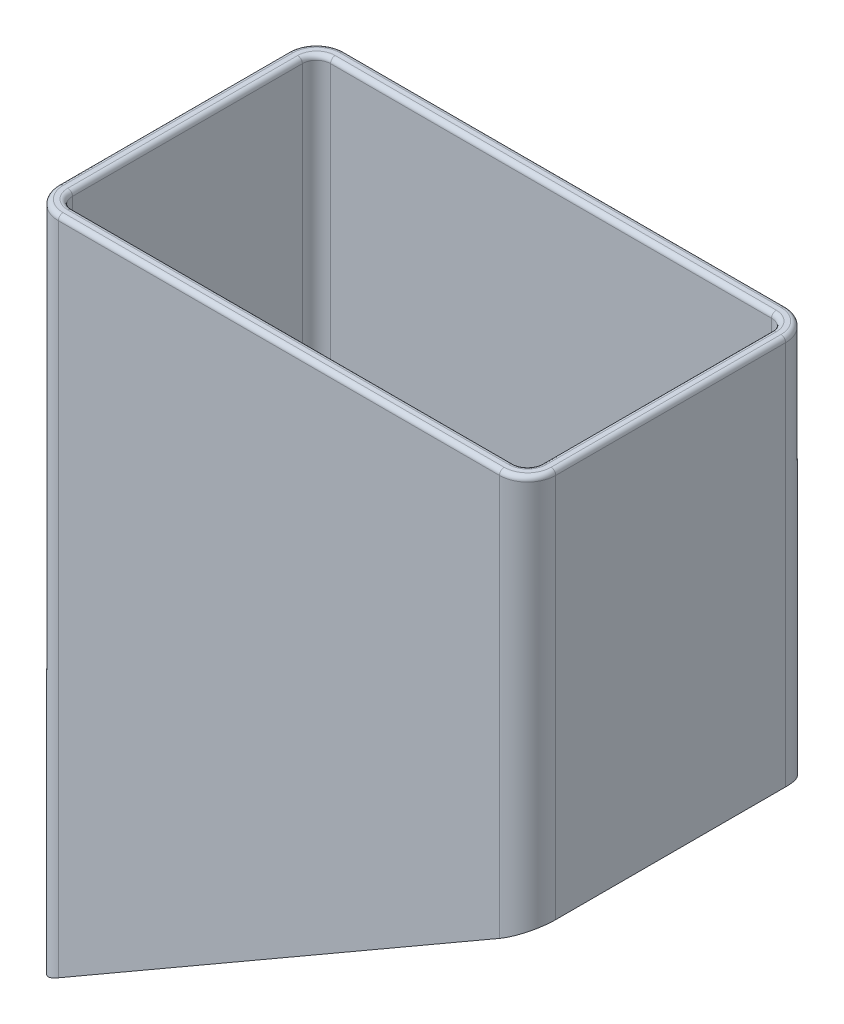
SolidWorks part; units mm, degrees
ref_plane "Front Plane" through (0, 0, 0) normal (0, 0, 1) x (1, 0, 0)
ref_plane "Top Plane" through (0, 0, 0) normal (0, 1, 0) x (1, 0, 0)
ref_plane "Right Plane" through (0, 0, 0) normal (1, 0, 0) x (0, 0, -1)
sketch "Sketch1" plane through (0, 0, 0) normal (0, 0, 1) x (1, 0, 0)
  line L0 (-50, 80) -> (-50, 0)
  line L1 (-50, 80) -> (50, 80)
  line L2 (-50, 0) -> (50, 0)
  line L3 (50, 80) -> (50, 0)
  line L4 (-50, 80) -> (50, 0) construction
  line L5 (-50, 0) -> (50, 80) construction
  line L6 (50, 80) -> (53, 80)
  line L7 (53, 80) -> (53, -3)
  line L8 (53, -3) -> (-53, -3)
  line L9 (-53, -3) -> (-53, 80)
  line L10 (-53, 80) -> (-50, 80)
  line L12 (-53, -3) -> (-50, -3) construction
  line L13 (-53, -3) -> (-53, 0) construction
  line L14 (-53, 0) -> (-50, 0) construction
  line L15 (-50, -3) -> (-50, 0) construction
  point P0 (32.4033, -1.1295)
  point P1 (0, 40)
  point P10 (-12.1047, -2.4419)
  point P13 (-8.686, -0.4186)
  point P14 (0, 0)
  dimension "D1" = 3
  dimension "D2" = 100
  dimension "D3" = 80
extrude "Boss-Extrude1" add sketch "Sketch1" along normal mid plane 55 contours L10 L9 L8 L7 L6 L3 L2 L0
sketch "Sketch3" plane through (0, 0, 0) normal (0, 0, 1) x (1, 0, 0)
  line L1 (-53, 80) -> (53, 80)
  line L2 (-53, 80) -> (-53, -3)
  line L3 (-53, -3) -> (53, -3)
  line L4 (53, 80) -> (53, -3)
extrude "Cut-Extrude1" cut sketch "Sketch3" against normal through all
sketch "Sketch4" plane through (0, 0, 27.5) normal (0, 0, 1) x (1, 0, 0)
  line L1 (-53, 80) -> (53, 80)
  line L2 (-53, 80) -> (-53, -3)
  line L3 (-53, -3) -> (53, -3)
  line L4 (53, 80) -> (53, -3)
extrude "Boss-Extrude2" add sketch "Sketch4" along normal blind 3
sketch "Sketch5" plane through (0, 0, 30.5) normal (0, 0, 1) x (1, 0, 0)
  line L0 (-53, -3) -> (-53, -64.1991)
  line L1 (-53, -64.1991) -> (53, -3)
  line L2 (53, -3) -> (-53, -3)
  dimension "D1" = 30
extrude "Boss-Extrude3" add sketch "Sketch5" against normal up to surface (30.5 mm away) up to plane "Front Plane"
fillet "Fillet1" radius 3 5 edges at (50, 40, 27.5) (-50, 40, 27.5) (-50, 0, 13.75) (50, 0, 13.75) (0, 0, 27.5)
fillet "Fillet2" radius 6 2 edges at (-53, 7.9004, 30.5) (53, 38.5, 30.5)
fillet "Fillet3" radius 1 10 edges at (50, 80, 12.25) (49.1213, 80, 26.6213) (-50, 80, 12.25) (-49.1213, 80, 26.6213) (-53, 80, 12.25) (-51.2426, 80, 28.7426) (0, 80, 30.5) (53, 80, 12.25) (0, 80, 27.5) (51.2426, 80, 28.7426)
sketch "Sketch8" plane through (14.549, -25.1997, 0) normal (0.5, -0.866, 0) x (0.866, 0.5, 0)
  line L0 (-77.9989, 0) -> (-57.9989, 0) construction
  line L1 (44.3993, 0) -> (-77.9989, 0) construction
  line L2 (44.3993, 0) -> (24.3993, 0) construction
  circle A0 centre (-57.9989, 0) radius 6
  circle A1 centre (24.3993, 0) radius 6
  dimension "D1" = 12
  dimension "D2" = 20
extrude "Cut-Extrude3" cut sketch "Sketch8" against normal through all from offset 10 offset against normal yes
hole_wizard "CSK for #10 Flat Head Machine Screw (100)2" positions "3DSketch2" profile "Sketch9" countersink size "#10" standard "ANSI Inch" end condition through all
sketch3d "3DSketch2"
  line L1 (-45.8756, -48.5389, 0) -> (-35.4833, -42.5389, 0) construction
  line L2 (25.4833, -7.3397, 0) -> (35.8756, -1.3397, 0) construction
  point P4 (-40.6795, -45.5389, 0)
  point P9 (-40.6795, -45.5389, 0)
  point P11 (30.6795, -4.3397, 0)
  point P16 (30.6795, -4.3397, 0)
sketch "Sketch9" plane through (-40.6795, -45.5389, 0) normal (0, 0, 1) x (-0.866, -0.5, 0)
  line L0 (0, 0) -> (0, 63)
  line L1 (0, 63) -> (2.8067, 63)
  line L2 (2.8067, 63) -> (2.8067, 1.7477)
  line L3 (2.8067, 1.7477) -> (4.8895, 0)
  line L5 (4.8895, 0) -> (0, 0)
  line L6 (-2.8067, 1.7477) -> (-4.8895, 0) construction
  line L11 (0, -6.35) -> (0, 107.95) construction
  dimension "Thru Hole Dia." = 5.6134
  dimension "Thru Hole Depth" = 63
  dimension "Near C'Sink Dia." = 9.779
  dimension "Near C'Sink Angle" = 100
mirror "Mirror1" about plane through (0, 0, 0) normal (0, 0, 1) of bodies 108
